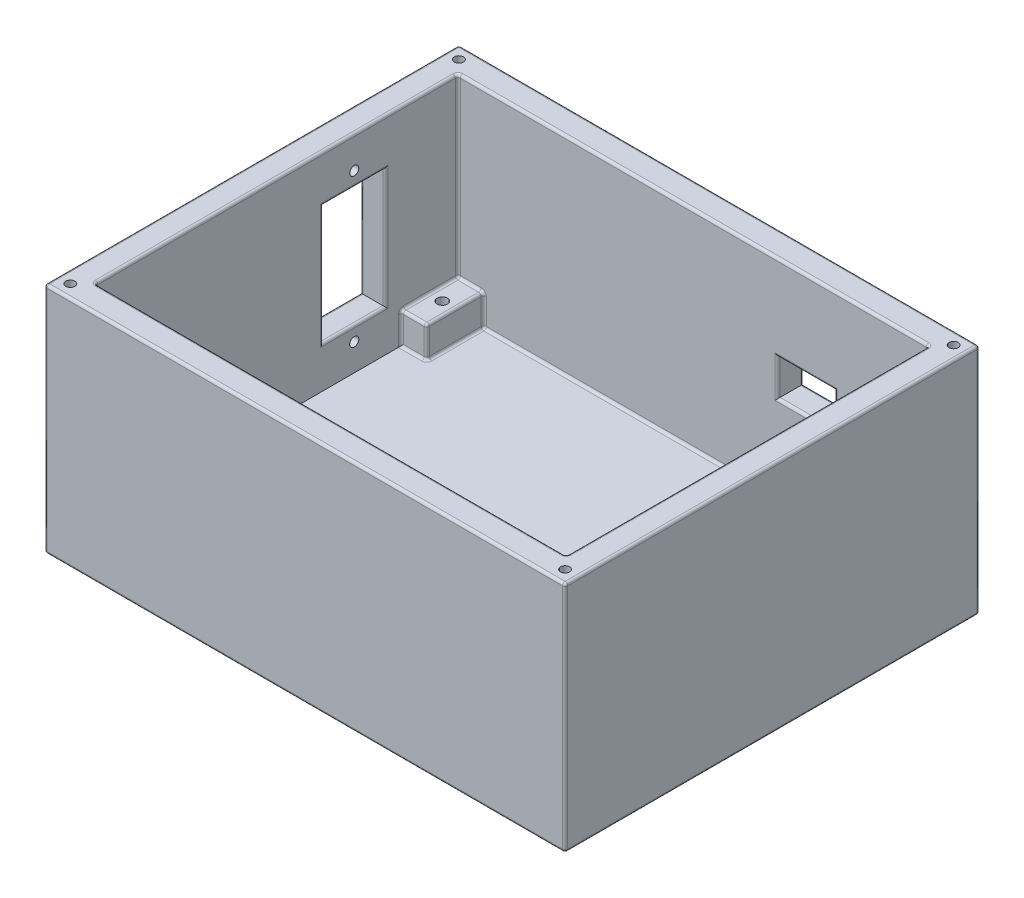
SolidWorks part; units mm, degrees
ref_plane "Plano frontal" through (0, 0, 0) normal (0, 0, 1) x (1, 0, 0)
ref_plane "Plano superior" through (0, 0, 0) normal (0, 1, 0) x (1, 0, 0)
ref_plane "Plano direito" through (0, 0, 0) normal (1, 0, 0) x (0, 0, -1)
sketch "Sketch1" plane through (0, 0, 0) normal (0, 1, 0) x (1, 0, 0)
  line L1 (-50.25, -40) -> (50.25, -40)
  line L2 (-50.25, -40) -> (-50.25, 40)
  line L3 (-50.25, 40) -> (50.25, 40)
  line L4 (50.25, -40) -> (50.25, 40)
  line L5 (-50.25, -40) -> (50.25, 40) construction
  line L6 (-50.25, 40) -> (50.25, -40) construction
  point P0 (0, 0)
  dimension "D1" = 80
  dimension "D2" = 100.5
extrude "Boss-Extrude1" add sketch "Sketch1" along normal blind 45
sketch "Sketch2" plane through (0, 45, 0) normal (0, 1, 0) x (1, 0, 0)
  line L0 (50.25, -40) -> (50.25, 40) construction
  line L1 (-45.45, -35) -> (45.45, -35)
  line L2 (-45.45, -35) -> (-45.45, 35)
  line L3 (-45.45, 35) -> (45.45, 35)
  line L4 (45.45, -35) -> (45.45, 35)
  line L5 (-45.45, -35) -> (45.45, 35) construction
  line L6 (-45.45, 35) -> (45.45, -35) construction
  line L7 (50.25, 40) -> (-50.25, 40) construction
  point P0 (0, 0)
  dimension "D1" = 4.8
  dimension "D2" = 5
extrude "Cut-Extrude1" cut sketch "Sketch2" against normal blind 40
sketch "Sketch3" plane through (0, 5, 0) normal (0, 1, 0) x (1, 0, 0)
  line L1 (45.45, 35) -> (36.45, 35)
  line L2 (45.45, 35) -> (45.45, 23)
  line L3 (45.45, 23) -> (36.45, 23)
  line L4 (36.45, 35) -> (36.45, 23)
  line L5 (45.45, -35) -> (36.45, -35)
  line L6 (45.45, -35) -> (45.45, -24)
  line L7 (45.45, -24) -> (36.45, -24)
  line L8 (36.45, -35) -> (36.45, -24)
  line L9 (-45.45, -35) -> (-40.45, -35)
  line L10 (-45.45, -35) -> (-45.45, -24)
  line L11 (-45.45, -24) -> (-40.45, -24)
  line L12 (-40.45, -35) -> (-40.45, -24)
  line L13 (-45.45, 35) -> (-40.45, 35)
  line L14 (-45.45, 35) -> (-45.45, 24)
  line L15 (-45.45, 24) -> (-40.45, 24)
  line L16 (-40.45, 35) -> (-40.45, 24)
  point P20 (-42.95, 24)
  dimension "D1" = 12
  dimension "D2" = 9
  dimension "D3" = 5
  dimension "D4" = 9
  dimension "D5" = 11
extrude "Boss-Extrude2" add sketch "Sketch3" along normal blind 6
sketch "Sketch4" plane through (0, 11, 0) normal (0, 1, 0) x (1, 0, 0)
  line L0 (36.45, 23) -> (45.45, 23) construction
  line L1 (36.45, 35) -> (36.45, 23) construction
  line L2 (45.45, -24) -> (36.45, -24) construction
  line L3 (36.45, -24) -> (36.45, -35) construction
  line L4 (-40.45, -24) -> (-45.45, -24) construction
  line L5 (-40.45, -35) -> (-40.45, -24) construction
  line L6 (-40.45, 24) -> (-40.45, 35) construction
  line L7 (-45.45, 24) -> (-40.45, 24) construction
  circle A1 centre (-42.95, -29.5) radius 1
  circle A2 centre (40.95, -29.5) radius 1
  circle A3 centre (40.95, 29) radius 1
  circle A4 centre (-42.95, 29.5) radius 1
  point P14 (40.95, 23)
  point P17 (36.45, 29)
  point P20 (40.95, -24)
  point P23 (36.45, -29.5)
  point P27 (-42.95, -24)
  point P30 (-40.45, -29.5)
  point P34 (-40.45, 29.5)
  point P37 (-42.95, 24)
  dimension "D1" = 2
extrude "Cut-Extrude2" cut sketch "Sketch4" against normal blind 8
sketch "Sketch5" plane through (0, 0, -40) normal (0, 0, -1) x (-1, 0, 0)
  line L0 (-27.25, 0) -> (-27.25, 45) construction
  line L1 (-50.25, 0) -> (50.25, 0) construction
  line L2 (-50.25, 45) -> (50.25, 45) construction
  line L3 (-50.25, 45) -> (-50.25, 0) construction
  line L4 (-50.25, 21.5) -> (50.25, 21.5) construction
  line L5 (50.25, 45) -> (50.25, 0) construction
  line L7 (-27.25, 21.5) -> (-16.25, 21.5)
  line L8 (-27.25, 21.5) -> (-27.25, 28.5)
  line L9 (-27.25, 28.5) -> (-16.25, 28.5)
  line L10 (-16.25, 21.5) -> (-16.25, 28.5)
  point P19 (-27.25, 21.5)
  dimension "D1" = 23
  dimension "D2" = 21.5
  dimension "D3" = 11
  dimension "D4" = 7
extrude "Cut-Extrude3" cut sketch "Sketch5" against normal up to next and the other way through all
sketch "Sketch6" plane through (0, 45, 0) normal (0, 1, 0) x (1, 0, 0)
  line L0 (-50.25, -40) -> (50.25, -40) construction
  line L1 (-50.25, 40) -> (-50.25, -40) construction
  line L2 (50.25, -40) -> (50.25, 40) construction
  line L3 (50.25, 40) -> (-50.25, 40) construction
  circle A0 centre (-47.75, 37.5) radius 0.875
  circle A1 centre (-47.75, -37.5) radius 0.875
  circle A2 centre (47.75, -37.5) radius 0.875
  circle A3 centre (47.75, 37.5) radius 0.875
  point P12 (0, 0)
  point P16 (0, 0)
  point P27 (0, 0)
  dimension "D1" = 1.75
  dimension "D2" = 2.5
  dimension "D3" = 2.5
  dimension "D4" = 2.5
  dimension "D5" = 2.5
extrude "Cut-Extrude4" cut sketch "Sketch6" against normal blind 10
sketch "Sketch8" plane through (-50.25, 0, 0) normal (-1, 0, 0) x (0, 0, 1)
  line L0 (-40, 13) -> (40, 13) construction
  line L1 (-40, 45) -> (-40, 0) construction
  line L2 (40, 45) -> (40, 0) construction
  line L3 (-21, 45) -> (-21, 0) construction
  line L4 (-40, 45) -> (40, 45) construction
  line L5 (-40, 0) -> (40, 0) construction
  line L7 (-21, 13) -> (-9, 13)
  line L8 (-21, 13) -> (-21, 36)
  line L9 (-21, 36) -> (-9, 36)
  line L10 (-9, 13) -> (-9, 36)
  point P12 (-21, 13)
  dimension "D1" = 19
  dimension "D2" = 13
  dimension "D3" = 23
  dimension "D4" = 12
extrude "Cut-Extrude5" cut sketch "Sketch8" against normal up to next
sketch "Sketch9" plane through (-50.25, 0, 0) normal (-1, 0, 0) x (0, 0, 1)
  line L0 (-15, 38.8) -> (-15, 10.2) construction
  line L1 (-9, 36) -> (-21, 36) construction
  line L2 (-21, 13) -> (-9, 13) construction
  circle A0 centre (-15, 38.8) radius 0.875
  circle A1 centre (-15, 10.2) radius 0.875
  point P1 (-15, 24.5)
  point P12 (-15, 36)
  dimension "D3" = 1.75
  dimension "D1" = 2.8
  dimension "D2" = 2.8
extrude "Cut-Extrude6" cut sketch "Sketch9" against normal blind 5
fillet "Fillet1" radius 0.5 74 edges at (-45.45, 11, -29.5) (-45.45, 8, 24) (-2, 5, 35) (40.95, 11, 35) (0, 45, 35) (-40.45, 8, 35) (40.95, 11, 24) (40.95, 5, 24) (36.45, 8, 24) (36.45, 11, 29.5) (36.45, 8, 35) (36.45, 5, 29.5) (40.95, 11, -23) (36.45, 11, -29) (36.45, 8, -23) (45.45, 5, 0.5) (45.45, 8, -23) (45.45, 11, -29) (45.45, 45, 0) (45.45, 28, 35) (45.45, 11, 29.5) (45.45, 8, 24) (21.75, 28.5, -35) (16.25, 25, -35) (21.75, 21.5, -35) (27.25, 25, -35) (-42.95, 11, -35) (0, 45, -35) (45.45, 28, -35) (40.95, 11, -35) (36.45, 8, -35) (-2, 5, -35) (-40.45, 11, -29.5) (-40.45, 8, -35) (-40.45, 5, -29.5) (-45.45, 8, -24) (-42.95, 11, -24) (-40.45, 8, -24) (-42.95, 5, -24) (50.25, 45, 0) (50.25, 0, 0) (-50.25, 22.5, 40) (0, 45, 40) (50.25, 22.5, 40) (0, 0, 40) (21.75, 21.5, -40) (16.25, 25, -40) (21.75, 28.5, -40) (27.25, 25, -40) (50.25, 22.5, -40) (0, 45, -40) (-50.25, 22.5, -40) (0, 0, -40) (40.95, 5, -23) (36.45, 5, -29) (-45.45, 28, -35) (-45.45, 36, -15) (-45.45, 24.5, -9) (-45.45, 24.5, -21) (-45.45, 13, -15) (-45.45, 28, 35) (-40.45, 5, 29.5) (-42.95, 5, 24) (-42.95, 11, 24) (-45.45, 11, 29.5) (-40.45, 11, 29.5) (-42.95, 11, 35) (-50.25, 45, 0) (-45.45, 45, 0) (-50.25, 0, 0) (-50.25, 36, -15) (-50.25, 24.5, -21) (-50.25, 24.5, -9) (-50.25, 13, -15)
